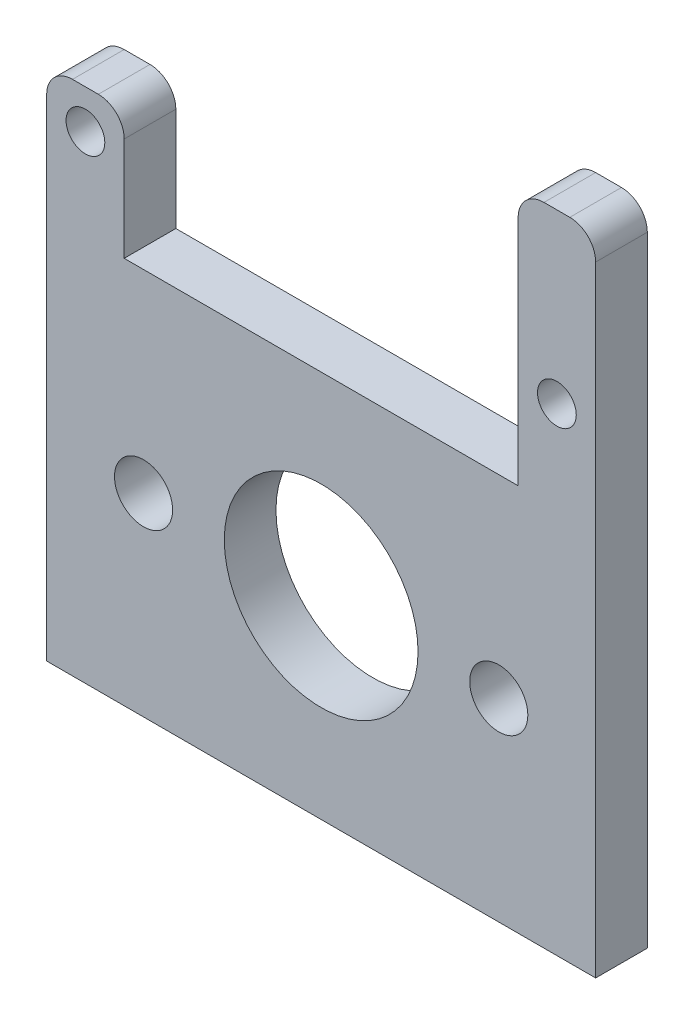
SolidWorks part; units mm, degrees
ref_plane "前视基准面" through (0, 0, 0) normal (0, 0, 1) x (1, 0, 0)
ref_plane "上视基准面" through (0, 0, 0) normal (0, 1, 0) x (1, 0, 0)
ref_plane "右视基准面" through (0, 0, 0) normal (1, 0, 0) x (0, 0, -1)
sketch "草图1" plane through (0, 0, 0) normal (0, 0, 1) x (1, 0, 0)
  line L0 (-15.0079, 17.6088) -> (21.4921, 17.6088) construction
  line L1 (-18.0079, 20.6088) -> (-18.0079, -13.6065)
  line L2 (-18.0079, 20.6088) -> (-12.0079, 20.6088)
  line L3 (-12.0079, 20.6088) -> (-12.0079, 10.6088)
  line L4 (-12.0079, 10.6088) -> (18.4921, 10.6088)
  line L5 (18.4921, 10.6088) -> (18.4921, 30.6088)
  line L6 (18.4921, 30.6088) -> (24.4921, 30.6088)
  line L7 (24.4921, 30.6088) -> (24.4921, -19.3912)
  line L8 (24.4921, -19.3912) -> (-18.0079, -19.3912)
  line L9 (-18.0079, -19.3912) -> (-18.0079, -13.6065)
  line L10 (-15.0079, 5.508) -> (-15.0079, -11.5442) construction
  line L11 (21.4921, 28.0031) -> (21.4921, 6.3233) construction
  line L12 (-24.9998, -4.3912) -> (41.1983, -4.3912) construction
  line L13 (3.2421, 28.8505) -> (3.2421, -25.5183) construction
  circle A0 centre (-15.0079, 17.6088) radius 1.5
  circle A1 centre (21.4921, 17.6088) radius 1.5
  circle A2 centre (-10.5079, -4.3912) radius 2.25
  circle A3 centre (16.9921, -4.3912) radius 2.25
  circle A4 centre (3.2421, -4.3912) radius 7.5
  dimension "D1" = 3
  dimension "D2" = 36.5
  dimension "D9" = 7.5
  dimension "D10" = 4.5
  dimension "D12" = 15
  dimension "D3" = 3
  dimension "D4" = 6
  dimension "D5" = 6
  dimension "D6" = 10
  dimension "D7" = 30
  dimension "D11" = 20
extrude "凸台-拉伸1" add sketch "草图1" along normal blind 4
fillet "圆角1" radius 2 4 edges at (24.4921, 30.6088, 2) (18.4921, 30.6088, 2) (-12.0079, 20.6088, 2) (-18.0079, 20.6088, 2)
